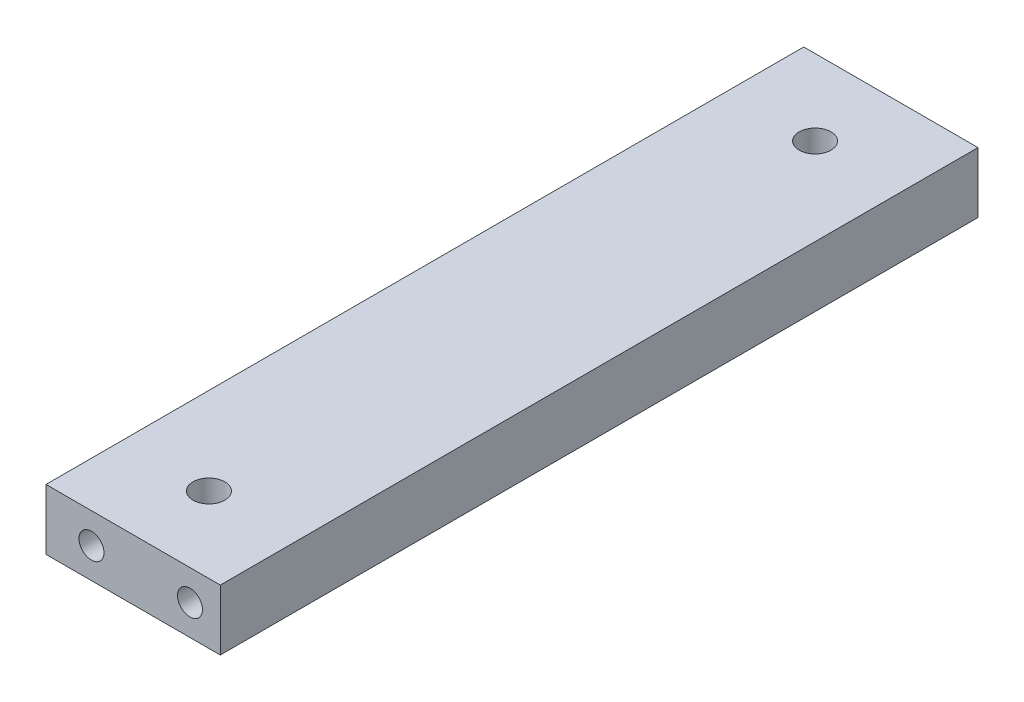
SolidWorks part; units mm, degrees
ref_plane "Front Plane" through (0, 0, 0) normal (0, 0, 1) x (1, 0, 0)
ref_plane "Top Plane" through (0, 0, 0) normal (0, 1, 0) x (1, 0, 0)
ref_plane "Right Plane" through (0, 0, 0) normal (1, 0, 0) x (0, 0, -1)
sketch "Sketch3" plane through (0, 0, 0) normal (0, 0, 1) x (1, 0, 0)
  line L1 (0, 0) -> (23, 0)
  line L2 (0, 0) -> (0, 8)
  line L3 (0, 8) -> (23, 8)
  line L4 (23, 0) -> (23, 8)
extrude "Extrude1" add sketch "Sketch3" along normal blind 100
sketch "Sketch4" plane through (0, 8, 0) normal (0, 1, 0) x (1, 0, 0)
  line L0 (11.5, 0) -> (11.5, -10) construction
  line L1 (23, 0) -> (0, 0) construction
  line L2 (11.5, -10) -> (11.5, -90) construction
  line L3 (11.5, -90) -> (11.5, -100) construction
  line L4 (23, -100) -> (0, -100) construction
hole_wizard "M5 Tapped Hole1" positions "3DSketch1" profile "Sketch6" tap size "M5" standard "DIN" end condition through all
sketch3d "3DSketch1"
  point P0 (11.5, 8, 90)
  point P3 (11.5, 8, 10)
sketch "Sketch6" plane through (11.5, 8, 90) normal (1, 0, 0) x (0, 0, 1)
  line L0 (0, 0) -> (0, 8)
  line L1 (0, 8) -> (2.1, 8)
  line L2 (2.1, 8) -> (2.1, 0)
  line L5 (2.1, 0) -> (0, 0)
  line L11 (0, -6.35) -> (0, 107.95) construction
  dimension "Thru Tap Drill Dia." = 4.2
  dimension "Thru Tap Drill Depth" = 8
cosmetic thread "Hole Thread1" parameters "D2"=5
cosmetic thread "Hole Thread2" parameters "D2"=5
sketch "Sketch7" plane through (0, 0, 100) normal (0, 0, 1) x (1, 0, 0)
  line L0 (23, 4) -> (19, 4) construction
  line L1 (23, 0) -> (23, 8) construction
  line L2 (19, 4) -> (6, 4) construction
  line L3 (6, 4) -> (0, 4) construction
  line L4 (0, 8) -> (0, 0) construction
sketch "Sketch8" plane through (0, 0, 0) normal (0, 0, -1) x (-1, 0, 0)
  line L0 (-23, 4) -> (-19, 4) construction
  line L1 (-23, 0) -> (-23, 8) construction
  line L2 (-19, 4) -> (-4, 4) construction
  line L3 (-4, 4) -> (0, 4) construction
  line L4 (0, 8) -> (0, 0) construction
hole_wizard "M4 Tapped Hole1" positions "3DSketch2" profile "Sketch9" tap size "M4" standard "DIN"
sketch3d "3DSketch2"
  point P0 (6, 4, 100)
  point P3 (19, 4, 100)
  point P6 (19, 4, 0)
  point P9 (4, 4, 0)
sketch "Sketch9" plane through (6, 4, 100) normal (1, 0, 0) x (0, -1, 0)
  line L0 (0, 0) -> (0, 10.9914)
  line L1 (0, 10.9914) -> (1.65, 10)
  line L2 (1.65, 10) -> (1.65, 0)
  line L5 (1.65, 0) -> (0, 0)
  line L10 (0, 10.9914) -> (-1.65, 10) construction
  line L11 (0, -6.35) -> (0, 107.95) construction
  dimension "Tap Drill Dia." = 3.3
  dimension "Tap Drill Depth" = 10
  dimension "Drill Angle" = 118
cosmetic thread "Hole Thread3" parameters "D1"=8, "D2"=4
cosmetic thread "Hole Thread4" parameters "D1"=8, "D2"=4
cosmetic thread "Hole Thread5" parameters "D1"=8, "D2"=4
cosmetic thread "Hole Thread6" parameters "D1"=8, "D2"=4
sketch "Sketch11" plane through (0, 0, 0) normal (-1, 0, 0) x (0, 0, 1)
  line L0 (0, 4) -> (100, 4) construction
  line L1 (0, 8) -> (0, 0) construction
  point P5 (4, 4)
hole_wizard "M3 Tapped Hole1" positions "3DSketch4" profile "Sketch12" tap size "M3" standard "DIN"
sketch3d "3DSketch4"
  point P0 (0, 4, 4)
sketch "Sketch12" plane through (0, 4, 4) normal (0, 1, 0) x (0, 0, 1)
  line L0 (0, 0) -> (0, 2.35)
  line L1 (0, 2.35) -> (1.25, 2.35)
  line L2 (1.25, 2.35) -> (1.25, 0)
  line L5 (1.25, 0) -> (0, 0)
  line L11 (0, -6.35) -> (0, 107.95) construction
  dimension "Thru Tap Drill Dia." = 2.5
  dimension "Thru Tap Drill Depth" = 2.35
cosmetic thread "Hole Thread7" parameters "D2"=3
